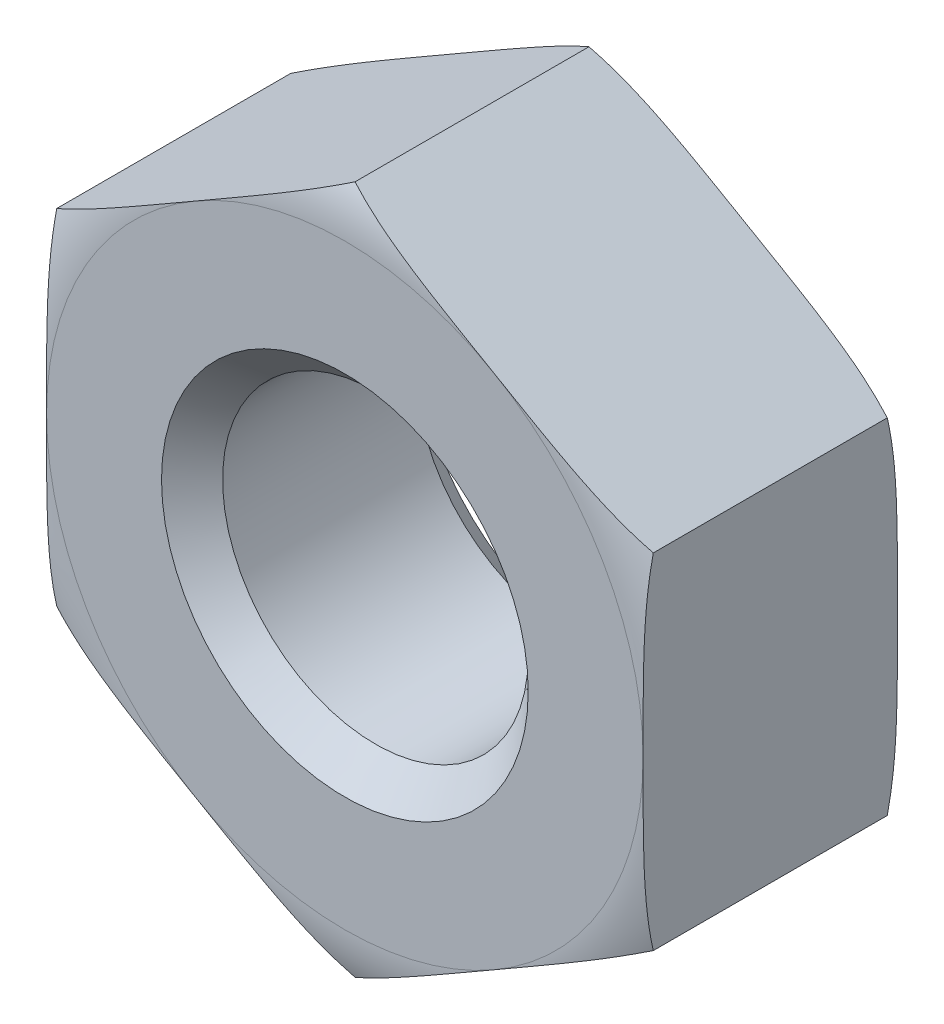
SolidWorks part; units mm, degrees
ref_plane "Front Plane" through (0, 0, 0) normal (0, 0, 1) x (1, 0, 0)
ref_plane "Top Plane" through (0, 0, 0) normal (0, 1, 0) x (1, 0, 0)
ref_plane "Right Plane" through (0, 0, 0) normal (1, 0, 0) x (0, 0, -1)
sketch "Sketch1" plane through (0, 0, 0) normal (0, 0, 1) x (1, 0, 0)
  line L1 (2.44, 1.4087) -> (0, 2.8175)
  line L2 (0, 2.8175) -> (-2.44, 1.4087)
  line L3 (-2.44, 1.4087) -> (-2.44, -1.4087)
  line L4 (-2.44, -1.4087) -> (0, -2.8175)
  line L5 (0, -2.8175) -> (2.44, -1.4087)
  line L6 (2.44, -1.4087) -> (2.44, 1.4087)
  circle A0 centre (0, 0) radius 2.44 construction
  circle A1 centre (0, 0) radius 1.25
  dimension "D1" = 2.5
  dimension "D2" = 4.88
extrude "Boss-Extrude1" add sketch "Sketch1" along normal blind 2.08
chamfer "Chamfer1" distance 0.25 angle 45 2 edges at (1.25, 0, 0) (1.25, 0, 2.08)
sketch "Sketch2" plane through (0, 0, 0) normal (0, 1, 0) x (1, 0, 0)
  line L0 (0, 0) -> (-2.44, 0) construction
  line L1 (-2.44, -2.08) -> (-2.44, 0) construction
  line L2 (0, -1.04) -> (-2.44, -1.04) construction
  line L3 (0, -2.08) -> (0, 0) construction
  line L4 (0, -1.04) -> (0, 1.437) construction
  line L5 (-3.3078, -0.6636) -> (-4.5008, -0.6636)
  line L6 (-4.5008, -0.6636) -> (-4.5008, 0.3612)
  line L7 (-4.5008, 0.3612) -> (-2.44, 0.3612)
  line L8 (-2.44, 0.3612) -> (-2.44, 0)
  line L9 (-2.44, -2.4412) -> (-2.44, -2.08)
  line L10 (-4.5008, -2.4412) -> (-2.44, -2.4412)
  line L11 (-4.5008, -1.4164) -> (-4.5008, -2.4412)
  line L12 (-3.3078, -1.4164) -> (-4.5008, -1.4164)
  arc A0 (-3.3078, -0.6636) -> (-2.44, 0) centre (-2.44, -0.8993) cw
  arc A1 (-3.3078, -1.4164) -> (-2.44, -2.08) centre (-2.44, -1.1807) ccw
  point P22 (-2.44, 0)
  point P23 (-2.44, 0)
  point P24 (-4, -0.3)
  point P25 (-4, -0.4405)
  point P26 (-3.3128, -0.4926)
revolve "Cut-Revolve1" cut sketch "Sketch2" angle 360 about L4
